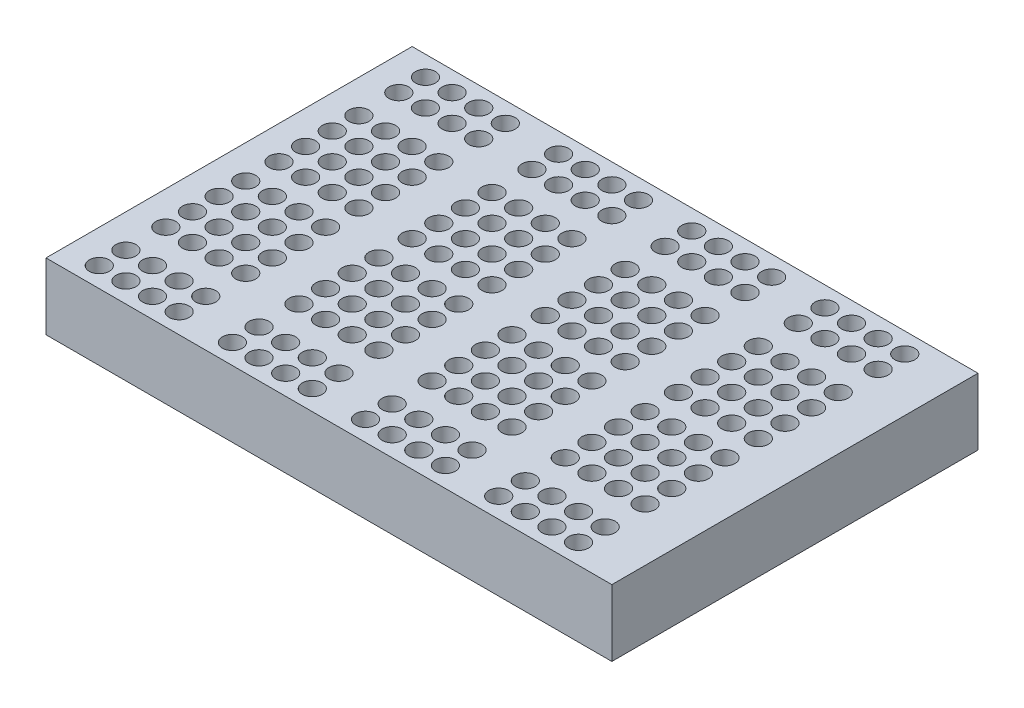
SolidWorks part; units mm, degrees
ref_plane "Front Plane" through (0, 0, 0) normal (0, 0, 1) x (1, 0, 0)
ref_plane "Top Plane" through (0, 0, 0) normal (0, 1, 0) x (1, 0, 0)
ref_plane "Right Plane" through (0, 0, 0) normal (1, 0, 0) x (0, 0, -1)
sketch "Sketch1" plane through (0, 0, 0) normal (0, 1, 0) x (1, 0, 0)
  line L1 (-42.5, 27.5) -> (42.5, 27.5)
  line L2 (-42.5, 27.5) -> (-42.5, -27.5)
  line L3 (-42.5, -27.5) -> (42.5, -27.5)
  line L4 (42.5, 27.5) -> (42.5, -27.5)
  line L5 (-42.5, 27.5) -> (42.5, -27.5) construction
  line L6 (-42.5, -27.5) -> (42.5, 27.5) construction
  point P0 (0, 0)
  dimension "D1" = 85
  dimension "D2" = 55
extrude "Boss-Extrude1" add sketch "Sketch1" along normal blind 10
sketch "Sketch2" plane through (0, 10, 0) normal (0, 1, 0) x (1, 0, 0)
  line L0 (42.5, 27.5) -> (-42.5, 27.5) construction
  line L1 (-42.5, 27.5) -> (-42.5, -27.5) construction
  line L2 (-52.1304, 0) -> (64.7415, 0) construction
  circle A0 centre (-37.5, 24.5) radius 1.5
  circle A1 centre (-33.5, 24.5) radius 1.5
  circle A2 centre (-29.5, 24.5) radius 1.5
  circle A3 centre (-25.5, 24.5) radius 1.5
  circle A4 centre (-17.5, 24.5) radius 1.5
  circle A5 centre (-13.5, 24.5) radius 1.5
  circle A6 centre (-9.5, 24.5) radius 1.5
  circle A7 centre (-5.5, 24.5) radius 1.5
  circle A8 centre (2.5, 24.5) radius 1.5
  circle A9 centre (6.5, 24.5) radius 1.5
  circle A10 centre (10.5, 24.5) radius 1.5
  circle A11 centre (14.5, 24.5) radius 1.5
  circle A12 centre (22.5, 24.5) radius 1.5
  circle A13 centre (26.5, 24.5) radius 1.5
  circle A14 centre (30.5, 24.5) radius 1.5
  circle A15 centre (34.5, 24.5) radius 1.5
  circle A16 centre (-37.5, 20.5) radius 1.5
  circle A17 centre (-33.5, 20.5) radius 1.5
  circle A18 centre (-29.5, 20.5) radius 1.5
  circle A19 centre (-25.5, 20.5) radius 1.5
  circle A20 centre (-17.5, 20.5) radius 1.5
  circle A21 centre (-13.5, 20.5) radius 1.5
  circle A22 centre (-9.5, 20.5) radius 1.5
  circle A23 centre (-5.5, 20.5) radius 1.5
  circle A24 centre (2.5, 20.5) radius 1.5
  circle A25 centre (6.5, 20.5) radius 1.5
  circle A26 centre (10.5, 20.5) radius 1.5
  circle A27 centre (14.5, 20.5) radius 1.5
  circle A28 centre (22.5, 20.5) radius 1.5
  circle A29 centre (26.5, 20.5) radius 1.5
  circle A30 centre (30.5, 20.5) radius 1.5
  circle A31 centre (34.5, 20.5) radius 1.5
  circle A32 centre (34.5, -20.5) radius 1.5
  circle A33 centre (30.5, -20.5) radius 1.5
  circle A34 centre (26.5, -20.5) radius 1.5
  circle A35 centre (22.5, -20.5) radius 1.5
  circle A36 centre (14.5, -20.5) radius 1.5
  circle A37 centre (10.5, -20.5) radius 1.5
  circle A38 centre (6.5, -20.5) radius 1.5
  circle A39 centre (2.5, -20.5) radius 1.5
  circle A40 centre (-5.5, -20.5) radius 1.5
  circle A41 centre (-9.5, -20.5) radius 1.5
  circle A42 centre (-13.5, -20.5) radius 1.5
  circle A43 centre (-17.5, -20.5) radius 1.5
  circle A44 centre (-25.5, -20.5) radius 1.5
  circle A45 centre (-29.5, -20.5) radius 1.5
  circle A46 centre (-33.5, -20.5) radius 1.5
  circle A47 centre (-37.5, -20.5) radius 1.5
  circle A48 centre (34.5, -24.5) radius 1.5
  circle A49 centre (30.5, -24.5) radius 1.5
  circle A50 centre (26.5, -24.5) radius 1.5
  circle A51 centre (22.5, -24.5) radius 1.5
  circle A52 centre (14.5, -24.5) radius 1.5
  circle A53 centre (10.5, -24.5) radius 1.5
  circle A54 centre (6.5, -24.5) radius 1.5
  circle A55 centre (2.5, -24.5) radius 1.5
  circle A56 centre (-5.5, -24.5) radius 1.5
  circle A57 centre (-9.5, -24.5) radius 1.5
  circle A58 centre (-13.5, -24.5) radius 1.5
  circle A59 centre (-17.5, -24.5) radius 1.5
  circle A60 centre (-25.5, -24.5) radius 1.5
  circle A61 centre (-29.5, -24.5) radius 1.5
  circle A62 centre (-33.5, -24.5) radius 1.5
  circle A63 centre (-37.5, -24.5) radius 1.5
  circle A64 centre (-37.5, 14.5) radius 1.5
  circle A65 centre (-33.5, 14.5) radius 1.5
  circle A66 centre (-29.5, 14.5) radius 1.5
  circle A67 centre (-25.5, 14.5) radius 1.5
  circle A68 centre (-17.5, 14.5) radius 1.5
  circle A69 centre (-13.5, 14.5) radius 1.5
  circle A70 centre (-9.5, 14.5) radius 1.5
  circle A71 centre (-5.5, 14.5) radius 1.5
  circle A72 centre (2.5, 14.5) radius 1.5
  circle A73 centre (6.5, 14.5) radius 1.5
  circle A74 centre (10.5, 14.5) radius 1.5
  circle A75 centre (14.5, 14.5) radius 1.5
  circle A76 centre (22.5, 14.5) radius 1.5
  circle A77 centre (26.5, 14.5) radius 1.5
  circle A78 centre (30.5, 14.5) radius 1.5
  circle A79 centre (34.5, 14.5) radius 1.5
  circle A80 centre (-37.5, 10.5) radius 1.5
  circle A81 centre (-33.5, 10.5) radius 1.5
  circle A82 centre (-29.5, 10.5) radius 1.5
  circle A83 centre (-25.5, 10.5) radius 1.5
  circle A84 centre (-17.5, 10.5) radius 1.5
  circle A85 centre (-13.5, 10.5) radius 1.5
  circle A86 centre (-9.5, 10.5) radius 1.5
  circle A87 centre (-5.5, 10.5) radius 1.5
  circle A88 centre (2.5, 10.5) radius 1.5
  circle A89 centre (6.5, 10.5) radius 1.5
  circle A90 centre (10.5, 10.5) radius 1.5
  circle A91 centre (14.5, 10.5) radius 1.5
  circle A92 centre (22.5, 10.5) radius 1.5
  circle A93 centre (26.5, 10.5) radius 1.5
  circle A94 centre (30.5, 10.5) radius 1.5
  circle A95 centre (34.5, 10.5) radius 1.5
  circle A96 centre (-37.5, 6.5) radius 1.5
  circle A97 centre (-33.5, 6.5) radius 1.5
  circle A98 centre (-29.5, 6.5) radius 1.5
  circle A99 centre (-25.5, 6.5) radius 1.5
  circle A100 centre (-17.5, 6.5) radius 1.5
  circle A101 centre (-13.5, 6.5) radius 1.5
  circle A102 centre (-9.5, 6.5) radius 1.5
  circle A103 centre (-5.5, 6.5) radius 1.5
  circle A104 centre (2.5, 6.5) radius 1.5
  circle A105 centre (6.5, 6.5) radius 1.5
  circle A106 centre (10.5, 6.5) radius 1.5
  circle A107 centre (14.5, 6.5) radius 1.5
  circle A108 centre (22.5, 6.5) radius 1.5
  circle A109 centre (26.5, 6.5) radius 1.5
  circle A110 centre (30.5, 6.5) radius 1.5
  circle A111 centre (34.5, 6.5) radius 1.5
  circle A112 centre (-37.5, 2.5) radius 1.5
  circle A113 centre (-33.5, 2.5) radius 1.5
  circle A114 centre (-29.5, 2.5) radius 1.5
  circle A115 centre (-25.5, 2.5) radius 1.5
  circle A116 centre (-17.5, 2.5) radius 1.5
  circle A117 centre (-13.5, 2.5) radius 1.5
  circle A118 centre (-9.5, 2.5) radius 1.5
  circle A119 centre (-5.5, 2.5) radius 1.5
  circle A120 centre (2.5, 2.5) radius 1.5
  circle A121 centre (6.5, 2.5) radius 1.5
  circle A122 centre (10.5, 2.5) radius 1.5
  circle A123 centre (14.5, 2.5) radius 1.5
  circle A124 centre (22.5, 2.5) radius 1.5
  circle A125 centre (26.5, 2.5) radius 1.5
  circle A126 centre (30.5, 2.5) radius 1.5
  circle A127 centre (34.5, 2.5) radius 1.5
  circle A128 centre (34.5, -2.5) radius 1.5
  circle A129 centre (30.5, -2.5) radius 1.5
  circle A130 centre (26.5, -2.5) radius 1.5
  circle A131 centre (22.5, -2.5) radius 1.5
  circle A132 centre (14.5, -2.5) radius 1.5
  circle A133 centre (10.5, -2.5) radius 1.5
  circle A134 centre (6.5, -2.5) radius 1.5
  circle A135 centre (2.5, -2.5) radius 1.5
  circle A136 centre (-5.5, -2.5) radius 1.5
  circle A137 centre (-9.5, -2.5) radius 1.5
  circle A138 centre (-13.5, -2.5) radius 1.5
  circle A139 centre (-17.5, -2.5) radius 1.5
  circle A140 centre (-25.5, -2.5) radius 1.5
  circle A141 centre (-29.5, -2.5) radius 1.5
  circle A142 centre (-33.5, -2.5) radius 1.5
  circle A143 centre (-37.5, -2.5) radius 1.5
  circle A144 centre (34.5, -6.5) radius 1.5
  circle A145 centre (30.5, -6.5) radius 1.5
  circle A146 centre (26.5, -6.5) radius 1.5
  circle A147 centre (22.5, -6.5) radius 1.5
  circle A148 centre (14.5, -6.5) radius 1.5
  circle A149 centre (10.5, -6.5) radius 1.5
  circle A150 centre (6.5, -6.5) radius 1.5
  circle A151 centre (2.5, -6.5) radius 1.5
  circle A152 centre (-5.5, -6.5) radius 1.5
  circle A153 centre (-9.5, -6.5) radius 1.5
  circle A154 centre (-13.5, -6.5) radius 1.5
  circle A155 centre (-17.5, -6.5) radius 1.5
  circle A156 centre (-25.5, -6.5) radius 1.5
  circle A157 centre (-29.5, -6.5) radius 1.5
  circle A158 centre (-33.5, -6.5) radius 1.5
  circle A159 centre (-37.5, -6.5) radius 1.5
  circle A160 centre (34.5, -10.5) radius 1.5
  circle A161 centre (30.5, -10.5) radius 1.5
  circle A162 centre (26.5, -10.5) radius 1.5
  circle A163 centre (22.5, -10.5) radius 1.5
  circle A164 centre (14.5, -10.5) radius 1.5
  circle A165 centre (10.5, -10.5) radius 1.5
  circle A166 centre (6.5, -10.5) radius 1.5
  circle A167 centre (2.5, -10.5) radius 1.5
  circle A168 centre (-5.5, -10.5) radius 1.5
  circle A169 centre (-9.5, -10.5) radius 1.5
  circle A170 centre (-13.5, -10.5) radius 1.5
  circle A171 centre (-17.5, -10.5) radius 1.5
  circle A172 centre (-25.5, -10.5) radius 1.5
  circle A173 centre (-29.5, -10.5) radius 1.5
  circle A174 centre (-33.5, -10.5) radius 1.5
  circle A175 centre (-37.5, -10.5) radius 1.5
  circle A176 centre (34.5, -14.5) radius 1.5
  circle A177 centre (30.5, -14.5) radius 1.5
  circle A178 centre (26.5, -14.5) radius 1.5
  circle A179 centre (22.5, -14.5) radius 1.5
  circle A180 centre (14.5, -14.5) radius 1.5
  circle A181 centre (10.5, -14.5) radius 1.5
  circle A182 centre (6.5, -14.5) radius 1.5
  circle A183 centre (2.5, -14.5) radius 1.5
  circle A184 centre (-5.5, -14.5) radius 1.5
  circle A185 centre (-9.5, -14.5) radius 1.5
  circle A186 centre (-13.5, -14.5) radius 1.5
  circle A187 centre (-17.5, -14.5) radius 1.5
  circle A188 centre (-25.5, -14.5) radius 1.5
  circle A189 centre (-29.5, -14.5) radius 1.5
  circle A190 centre (-33.5, -14.5) radius 1.5
  circle A191 centre (-37.5, -14.5) radius 1.5
  dimension "D1" = 3
  dimension "D2" = 3
  dimension "D3" = 5
  dimension "D4" = 4
  dimension "D5" = 4
  dimension "D6" = 2
  dimension "D7" = 2
  dimension "D8" = 2
extrude "Cut-Extrude1" cut sketch "Sketch2" against normal blind 7
